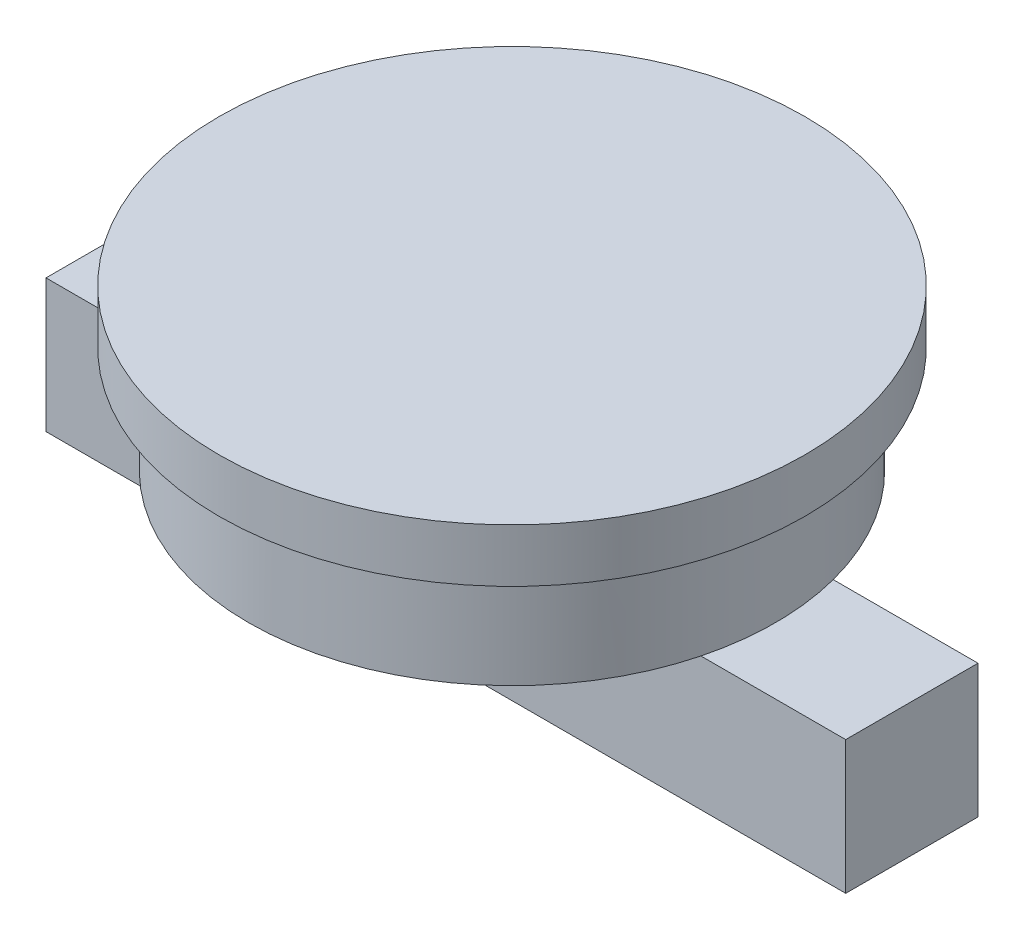
SolidWorks part; units mm, degrees
ref_plane "Front Plane" through (0, 0, 0) normal (0, 0, 1) x (1, 0, 0)
ref_plane "Top Plane" through (0, 0, 0) normal (0, 1, 0) x (1, 0, 0)
ref_plane "Right Plane" through (0, 0, 0) normal (1, 0, 0) x (0, 0, -1)
sketch "Sketch2" plane through (0, 0, 0) normal (0, 1, 0) x (1, 0, 0)
  circle A0 centre (0, 0) radius 1100
extrude "Boss-Extrude1" add sketch "Sketch2" against normal blind 200
sketch "Sketch3" plane through (0, -200, 0) normal (0, -1, 0) x (1, 0, 0)
  circle A0 centre (0, 0) radius 989.4418
extrude "Boss-Extrude2" add sketch "Sketch3" along normal blind 401
sketch "Sketch4" plane through (0, -601, 0) normal (0, -1, 0) x (1, 0, 0)
  line L1 (-1501.265, -248.3401) -> (1501.265, -248.3401)
  line L2 (-1501.265, -248.3401) -> (-1501.265, 248.3401)
  line L3 (-1501.265, 248.3401) -> (1501.265, 248.3401)
  line L4 (1501.265, -248.3401) -> (1501.265, 248.3401)
  point P0 (0, 0)
extrude "Boss-Extrude3" add sketch "Sketch4" along normal blind 500
